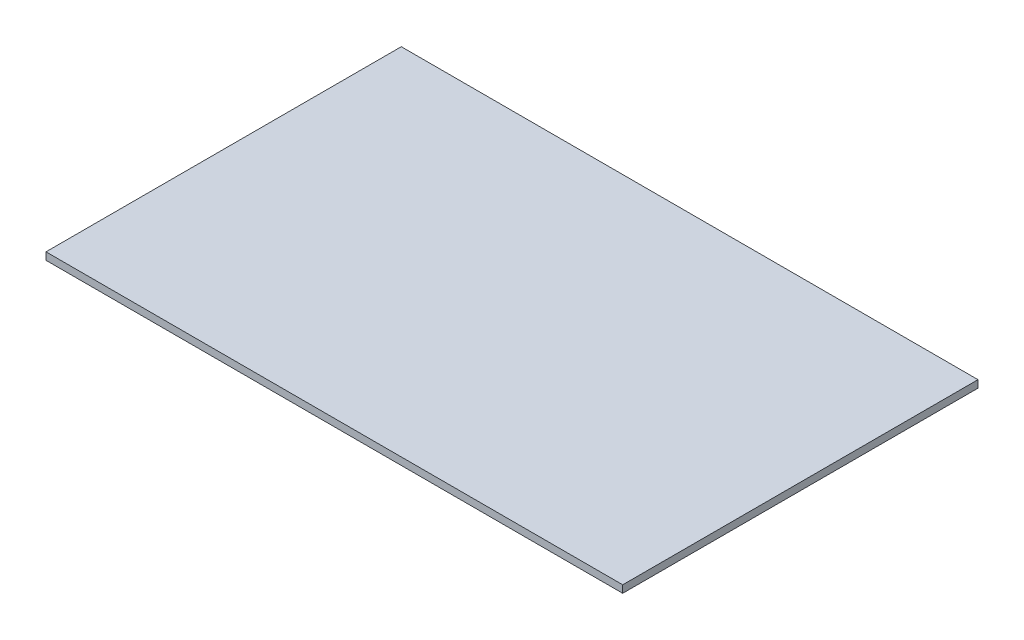
SolidWorks part; units mm, degrees
material "Acrylic (Medium-high impact)"
ref_plane "Front Plane" through (0, 0, 0) normal (0, 0, 1) x (1, 0, 0)
ref_plane "Top Plane" through (0, 0, 0) normal (0, 1, 0) x (1, 0, 0)
ref_plane "Right Plane" through (0, 0, 0) normal (1, 0, 0) x (0, 0, -1)
sketch "Sketch1" plane through (0, 0, 0) normal (0, 1, 0) x (1, 0, 0)
  line L1 (-117.094, 72.136) -> (117.094, 72.136)
  line L2 (-117.094, 72.136) -> (-117.094, -72.136)
  line L3 (-117.094, -72.136) -> (117.094, -72.136)
  line L4 (117.094, 72.136) -> (117.094, -72.136)
  line L5 (-117.094, 72.136) -> (117.094, -72.136) construction
  line L6 (-117.094, -72.136) -> (117.094, 72.136) construction
  point P0 (0, 0)
  dimension "D1" = 234.188
  dimension "D2" = 144.272
extrude "Boss-Extrude1" add sketch "Sketch1" along normal blind 3
